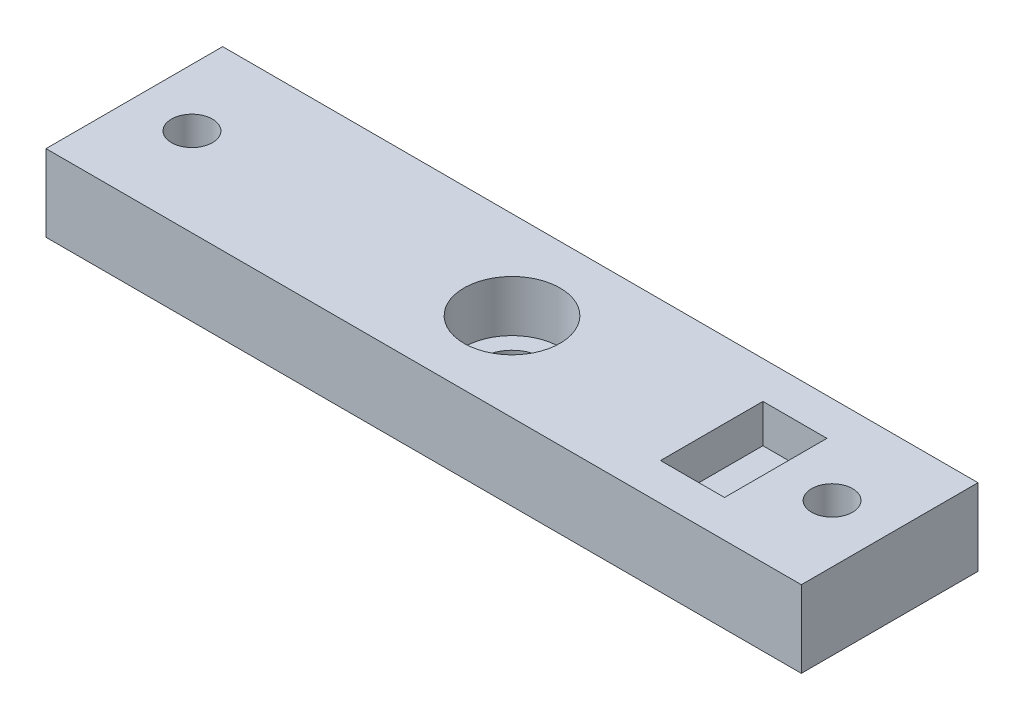
SolidWorks part; units mm, degrees
ref_plane "Plan de face" through (0, 0, 0) normal (0, 0, 1) x (1, 0, 0)
ref_plane "Plan de dessus" through (0, 0, 0) normal (0, 1, 0) x (1, 0, 0)
ref_plane "Plan de droite" through (0, 0, 0) normal (1, 0, 0) x (0, 0, -1)
sketch "Esquisse1" plane through (0, 0, 0) normal (0, 1, 0) x (1, 0, 0)
  line L0 (29.5, 6.9) -> (0, 6.9) construction
  line L1 (0, 0) -> (29.5, 0)
  line L2 (0, 0) -> (0, 13.8)
  line L3 (0, 13.8) -> (29.5, 13.8)
  line L4 (29.5, 0) -> (29.5, 13.8)
  circle A0 centre (25, 6.9) radius 1.6
  dimension "D4" = 3.2
  dimension "D1" = 13.8
  dimension "D2" = 29.5
  dimension "D3" = 25
extrude "Boss.-Extru.1" add sketch "Esquisse1" along normal blind 6
sketch "Esquisse2" plane through (0, 6, 0) normal (0, 1, 0) x (1, 0, 0)
  line L0 (0, 13.8) -> (0, 0) construction
  circle A0 centre (0, 6.9) radius 2.35
  dimension "D1" = 4.7
extrude "Enlèv. mat.-Extru.1" cut sketch "Esquisse2" against normal through all
sketch "Esquisse3" plane through (0, 6, 0) normal (0, 1, 0) x (1, 0, 0)
  circle A0 centre (0, 6.9) radius 3.75
  dimension "D1" = 7.5
extrude "Enlèv. mat.-Extru.2" cut sketch "Esquisse3" against normal blind 4
mirror "Symétrie1" about plane through (0, 6, 0) normal (1, 0, 0) of bodies 105
sketch "Esquisse5" plane through (0, 6, 0) normal (0, -1, 0) x (1, 0, 0)
  line L0 (29.5, 0) -> (29.5, -13.8) construction
  line L1 (15.6, -2.9) -> (20.6, -2.9)
  line L2 (15.6, -2.9) -> (15.6, -10.9)
  line L3 (15.6, -10.9) -> (20.6, -10.9)
  line L4 (20.6, -2.9) -> (20.6, -10.9)
  line L5 (29.5, 0) -> (29.5, -13.8)
  point P6 (29.5, -6.9)
  point P7 (20.6, -6.9)
  point P8 (18.1, -2.9)
  point P9 (0, 0)
  point P10 (18.1, -2.9)
  dimension "D1" = 5
  dimension "D2" = 8
  dimension "D3" = 11.4
extrude "Enlèv. mat.-Extru.3" cut sketch "Esquisse5" along normal blind 3 contours L1 L4 L3 L2
equation "\"D2@Esquisse1\"=59/2"
